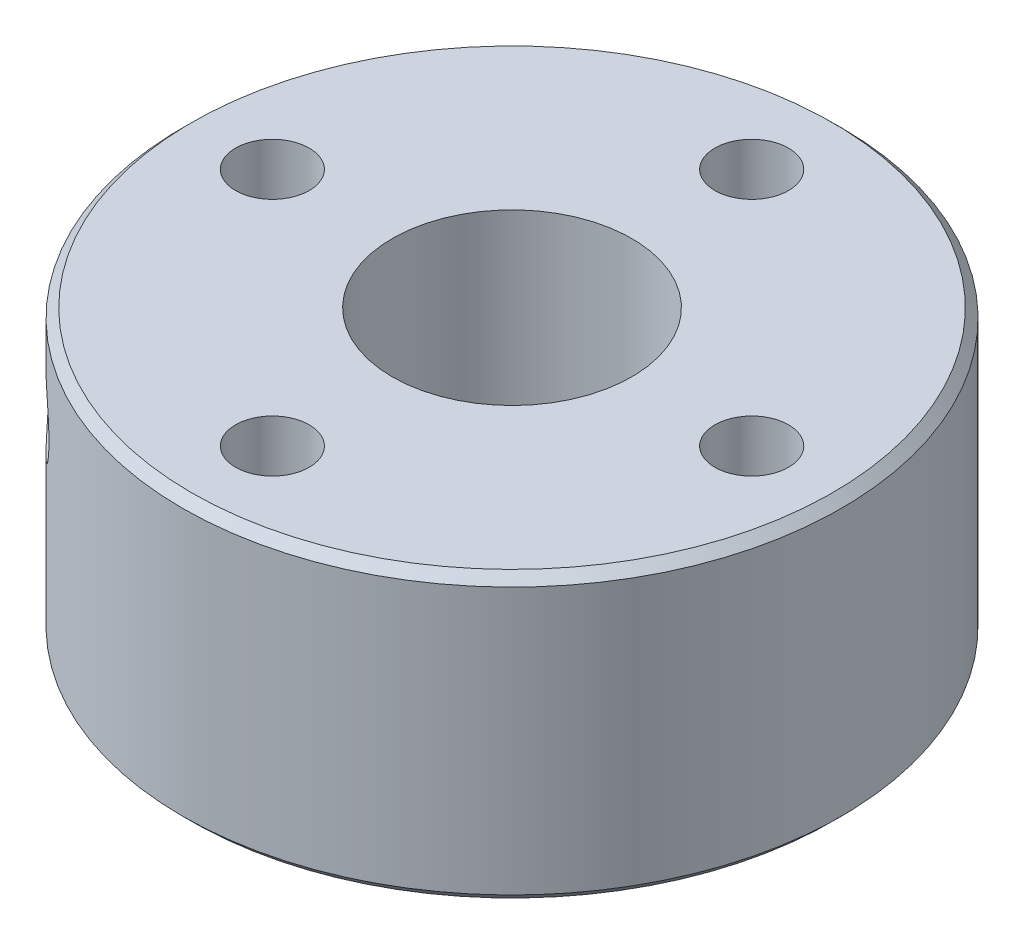
SolidWorks part; units mm, degrees
material "Lega 1060"
ref_plane "Piano frontale" through (0, 0, 0) normal (0, 0, 1) x (1, 0, 0)
ref_plane "Piano superiore" through (0, 0, 0) normal (0, 1, 0) x (1, 0, 0)
ref_plane "Piano destro" through (0, 0, 0) normal (1, 0, 0) x (0, 0, -1)
ref_plane "Piano1" through (0, 0, 0) normal (0, 0, -1) x (-1, 0, 0)
sketch "Schizzo1" plane through (0, 0, 0) normal (0, 0, -1) x (-1, 0, 0)
  line L0 (-11, 3.5) -> (0, 3.5)
  line L1 (0, 3.5) -> (0, 13)
  line L2 (0, 13) -> (-11, 13)
  line L3 (-11, 13) -> (-11, 3.5)
  line L4 (0, 3.5) -> (0, 13) construction
revolve "Rivoluzione1" add sketch "Schizzo1" angle 360 about L4
sketch "Schizzo2" plane through (0, 3.5, 0) normal (0, -1, 0) x (1, 0, 0)
  circle A0 centre (0, 0) radius 4.75
extrude "Estrusione-Estrusione1" add sketch "Schizzo2" along normal blind 3.5
hole_wizard "Foro per Vite M2-1" positions "Schizzo4" profile "Schizzo3" hole size "M2" standard "Ansi Metric"
sketch "Schizzo4" plane through (0, 13, 0) normal (0, 1, 0) x (1, 0, 0)
  point P0 (0, 8)
  point P1 (-8, 0)
  point P2 (0, -8)
  point P3 (8, 0)
sketch "Schizzo3" plane through (0, 13, -8) normal (1, 0, 0) x (0, 0, 1)
  line L0 (0, 0) -> (0, 13)
  line L1 (0, 13) -> (1.2295, 13)
  line L2 (1.2295, 13) -> (1.2295, 0)
  line L5 (1.2295, 0) -> (0, 0)
  line L11 (0, -6.35) -> (0, 107.95) construction
  dimension "Thru Hole Dia." = 2.459
  dimension "Thru Hole Depth" = 13
hole_wizard "Foro lamato per Vite M3.5 a testa esagonale-1" positions "Schizzo6" profile "Schizzo5" counterbore size "M3.5" standard "Ansi Metric"
sketch "Schizzo6" plane through (0, 13, 0) normal (0, 1, 0) x (1, 0, 0)
  point P0 (0, 0)
sketch "Schizzo5" plane through (0, 13, 0) normal (1, 0, 0) x (0, 0, 1)
  line L0 (0, 0) -> (0, 13)
  line L1 (0, 13) -> (2, 13)
  line L3 (2, 13) -> (2, 8.5)
  line L4 (2, 8.5) -> (4, 8.5)
  line L5 (4, 8.5) -> (4, 0)
  line L7 (4, 0) -> (0, 0)
  line L11 (0, -6.35) -> (0, 107.95) construction
  dimension "Thru Hole Dia." = 4
  dimension "Thru Hole Depth" = 13
  dimension "C'Bore Dia." = 8
  dimension "C'Bore Depth" = 8.5
ref_plane "Piano2" through (-2.6915, 0, 2.6915) normal (0.7071, 0, -0.7071) x (-0.7071, 0, -0.7071)
hole_wizard "Foro per Vite M2-2" positions "Schizzo8" profile "Schizzo7" hole size "M2" standard "Ansi Metric"
sketch "Schizzo8" plane through (-2.6915, 0, 2.6915) normal (0.7071, 0, -0.7071) x (-0.7071, 0, -0.7071)
  point P0 (0, 10)
sketch "Schizzo7" plane through (-2.6915, 10, 2.6915) normal (0, 1, 0) x (-0.7071, 0, -0.7071)
  line L0 (0, 0) -> (0, 11.75)
  line L1 (0, 11.75) -> (1.2295, 11.75)
  line L2 (1.2295, 11.75) -> (1.2295, 0)
  line L5 (1.2295, 0) -> (0, 0)
  line L11 (0, -6.35) -> (0, 107.95) construction
  dimension "Thru Hole Dia." = 2.459
  dimension "Thru Hole Depth" = 11.75
chamfer "Smusso1" distance 0.3 angle 45 3 edges at (0, 0, -4.75) (0, 3.5, 11) (0, 13, 11)
